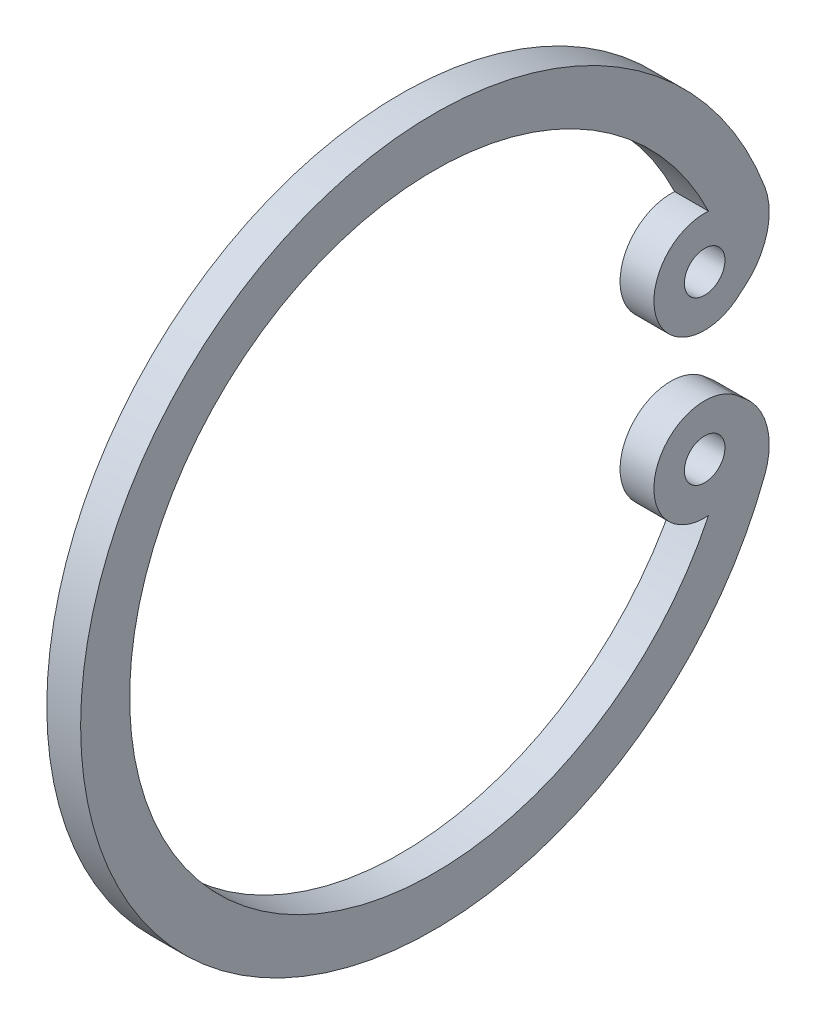
SolidWorks part; units mm, degrees
material "Plain Carbon Steel"
ref_plane "Front Plane" through (0, 0, 0) normal (0, 0, 1) x (1, 0, 0)
ref_plane "Top Plane" through (0, 0, 0) normal (0, 1, 0) x (1, 0, 0)
ref_plane "Right Plane" through (0, 0, 0) normal (1, 0, 0) x (0, 0, -1)
ref_plane "Plane1" through (19, 0, 0) normal (1, 0, 0) x (0, 0, -1)
sketch "Sketch1" plane through (19, 0, 0) normal (1, 0, 0) x (0, 0, -1)
  line L0 (-1.0829, 1.2142) -> (-0.8063, 1.4448)
  line L1 (-0.8063, -1.4451) -> (-1.0822, -1.2136)
  arc A0 (-1.8869, 3.8965) -> (-1.0829, 1.2142) centre (-2.0005, 2.4008) ccw
  arc A1 (-0.8063, 1.4448) -> (-0.2201, 3.6816) centre (-2.0918, 2.9769) ccw
  arc A2 (-0.2201, 3.6816) -> (-0.2201, -3.6818) centre (-9.9996, -0.0001) ccw
  arc A3 (-0.2201, -3.6818) -> (-0.8063, -1.4451) centre (-2.0918, -2.9772) ccw
  arc A4 (-1.0822, -1.2136) -> (-1.8869, -3.8967) centre (-2.0004, -2.4004) ccw
  arc A5 (-1.8869, -3.8967) -> (-1.8869, 3.8965) centre (-9.9996, -0.0001) cw
  circle A6 centre (-2, -2.4) radius 0.6
  circle A7 centre (-2, 2.4) radius 0.6
extrude "Boss-Extrude1" add sketch "Sketch1" against normal blind 1
scale "Scale2" scale about centroid uniform scaling yes scale factor 0.277778
